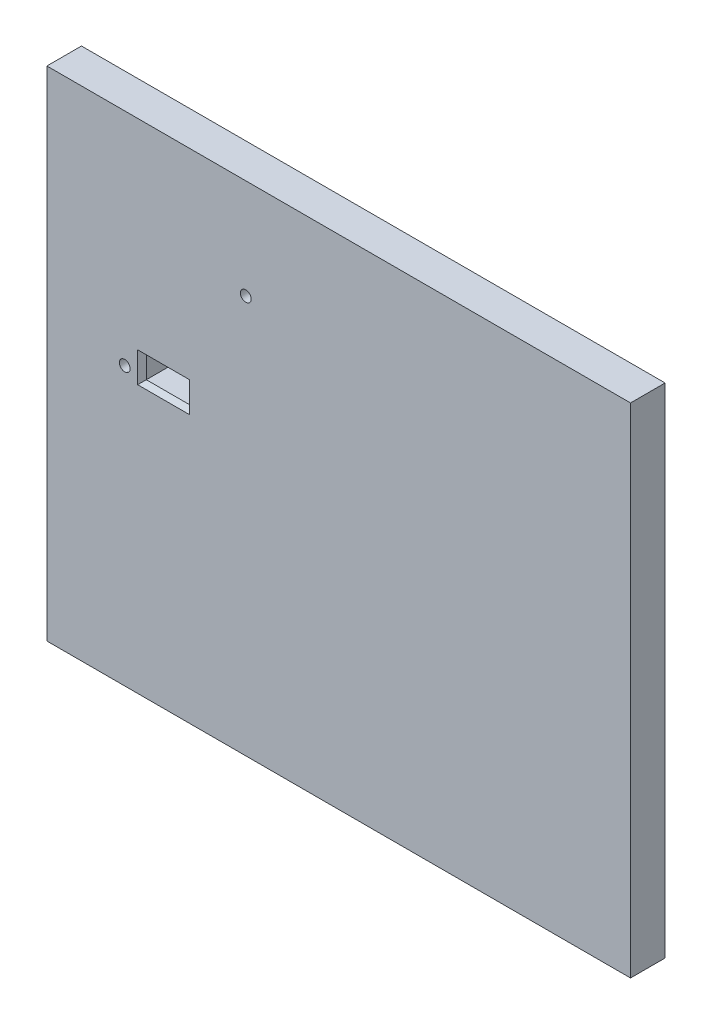
SolidWorks part; units mm, degrees
ref_plane "Front Plane" through (0, 0, 0) normal (0, 0, 1) x (1, 0, 0)
ref_plane "Top Plane" through (0, 0, 0) normal (0, 1, 0) x (1, 0, 0)
ref_plane "Right Plane" through (0, 0, 0) normal (1, 0, 0) x (0, 0, -1)
sketch "Sketch1" plane through (0, 0, 0) normal (0, 0, 1) x (1, 0, 0)
  line L4 (67.5, -20) -> (-67.5, -20) construction
  line L5 (-67.5, 95.1988) -> (67.5, 95.1988) construction
  line L6 (-67.5, 95.1988) -> (-67.5, -20) construction
  line L7 (67.5, 95.1988) -> (67.5, -20) construction
  line L8 (67.5, 95.1988) -> (-67.5, 95.1988)
  line L9 (-67.5, 95.1988) -> (-67.5, -20)
  line L10 (-67.5, -20) -> (67.5, -20)
  line L11 (67.5, -20) -> (67.5, 95.1988)
extrude "Boss-Extrude1" add sketch "Sketch1" along normal blind 8 from surface at 65
sketch "Sketch2" plane through (0, 0, 73) normal (0, 0, 1) x (1, 0, 0)
  line L0 (-45.5, 47.846) -> (-45.5, 42.846)
  line L1 (-45.5, 42.846) -> (-35.5, 42.846)
  line L2 (-45.5, 47.846) -> (-35.5, 47.846)
  line L3 (-35.5, 47.846) -> (-35.5, 42.846)
  line L4 (-67.5, -20) -> (-67.5, 95.1988) construction
  line L6 (67.5, -20) -> (-67.5, -20) construction
  dimension "D1" = 5
  dimension "D2" = 10
  dimension "D3" = 22
  dimension "D4" = 67.846
extrude "Cut-Extrude1" cut sketch "Sketch2" against normal through all
sketch "Sketch3" plane through (0, 0, 73) normal (0, 0, 1) x (1, 0, 0)
  line L0 (-45.5, 47.846) -> (-45.5, 42.846) construction
  line L1 (-45.5, 42.846) -> (-35.5, 42.846) construction
  line L2 (-35.5, 42.846) -> (-35.5, 47.846) construction
  line L4 (-35.5, 47.846) -> (-45.5, 47.846) construction
  circle A0 centre (-21.5, 72.116) radius 1.25
  circle A1 centre (-49.5, 44.176) radius 1.25
  dimension "D1" = 4
  dimension "D4" = 29.27
  dimension "D2" = 3.67
  dimension "D3" = 14
extrude "Cut-Extrude2" cut sketch "Sketch3" against normal through all
chamfer "Chamfer2" distance 1 angle 45 4 edges at (-35.5, 45.346, 73) (-40.5, 42.846, 73) (-45.5, 45.346, 73) (-40.5, 47.846, 73)
